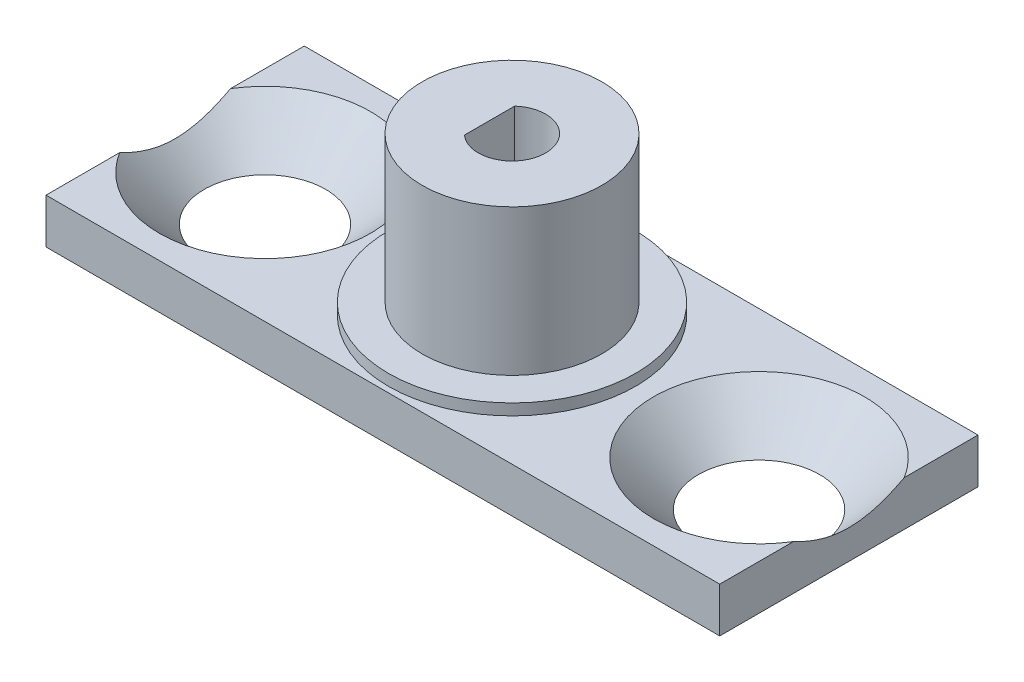
SolidWorks part; units mm, degrees
ref_plane "Front Plane" through (0, 0, 0) normal (0, 0, 1) x (1, 0, 0)
ref_plane "Top Plane" through (0, 0, 0) normal (0, 1, 0) x (1, 0, 0)
ref_plane "Right Plane" through (0, 0, 0) normal (1, 0, 0) x (0, 0, -1)
sketch "Sketch1" plane through (0, 0, 0) normal (0, 1, 0) x (1, 0, 0)
  line L1 (-15, 5.75) -> (15, 5.75)
  line L2 (-15, 5.75) -> (-15, -5.75)
  line L3 (-15, -5.75) -> (15, -5.75)
  line L4 (15, 5.75) -> (15, -5.75)
  line L5 (0, -5.75) -> (0, 5.75) construction
  line L6 (-15, 0) -> (15, 0) construction
  point P4 (0, 0)
  point P120 (0, 0)
  dimension "D1" = 30
  dimension "D2" = 11.5
extrude "Boss-Extrude1" add sketch "Sketch1" along normal blind 2
sketch "Sketch2" plane through (0, 2, 0) normal (0, 1, 0) x (1, 0, 0)
  circle A0 centre (0, 0) radius 5.5
  point P3 (0, 0)
  dimension "D1" = 11
extrude "Boss-Extrude2" add sketch "Sketch2" along normal blind 0.5
sketch "Sketch3" plane through (0, 2.5, 0) normal (0, 1, 0) x (1, 0, 0)
  circle A0 centre (0, 0) radius 4
  dimension "D1" = 8
extrude "Boss-Extrude3" add sketch "Sketch3" along normal blind 6.5
sketch "Sketch4" plane through (0, 9, 0) normal (0, 1, 0) x (1, 0, 0)
  line L0 (-1, 1.118) -> (-1, -1.118)
  line L1 (1.5, 0) -> (1.5, 2.2094) construction
  arc A0 (-1, -1.118) -> (-1, 1.118) centre (0, 0) ccw
  dimension "D1" = 3
  dimension "D2" = 2.5
extrude "Cut-Extrude1" cut sketch "Sketch4" against normal blind 7
hole_wizard "CSK for M4 Countersunk Flat Head Screw1" positions "Sketch9" profile "Sketch6" countersink size "M4" standard "ISO"
sketch "Sketch9" plane through (0, 2, 0) normal (0, 1, 0) x (1, 0, 0)
  line L0 (-4.95, 0) -> (4.95, 0) construction
  line L1 (0, -4.95) -> (0, 4.95) construction
  point P0 (11, 0)
  point P10 (0, 0)
  point P11 (-11, 0)
  dimension "D1" = 11
sketch "Sketch6" plane through (11, 2, 0) normal (1, 0, 0) x (0, 0, 1)
  line L0 (0, 0) -> (0, 3.3519)
  line L1 (0, 3.3519) -> (2.25, 2)
  line L2 (2.25, 2) -> (2.25, 2.45)
  line L3 (2.25, 2.45) -> (4.7, 0)
  line L5 (4.7, 0) -> (0, 0)
  line L6 (-2.25, 2.45) -> (-4.7, 0) construction
  line L10 (0, 3.3519) -> (-2.25, 2) construction
  line L11 (0, -6.35) -> (0, 107.95) construction
  dimension "Hole Dia." = 4.5
  dimension "Hole Depth" = 2
  dimension "Near C'Sink Dia." = 9.4
  dimension "Near C'Sink Angle" = 90
  dimension "Drill Angle" = 118
